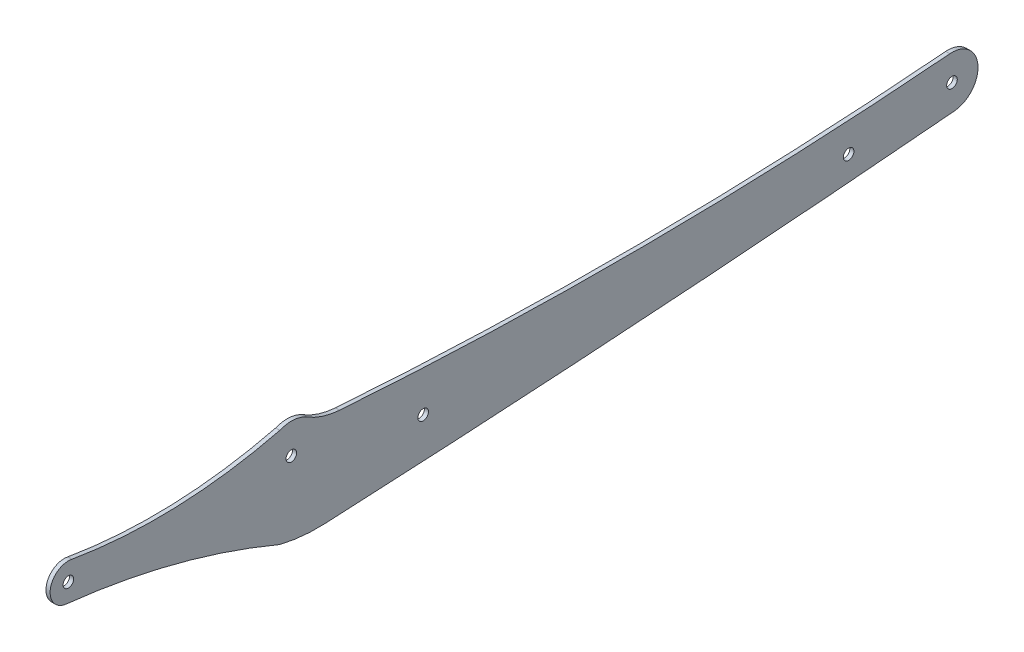
SolidWorks part; units mm, degrees
ref_plane "前基準面" through (0, 0, 0) normal (0, 0, 1) x (1, 0, 0)
ref_plane "上基準面" through (0, 0, 0) normal (0, 1, 0) x (1, 0, 0)
ref_plane "右基準面" through (0, 0, 0) normal (1, 0, 0) x (0, 0, -1)
sketch "草圖1" plane through (0, 0, 0) normal (1, 0, 0) x (0, 0, -1)
  line L0 (-207.7239, 114.2461) -> (-126.7284, 113.3952) construction
  line L1 (-126.7284, 113.3952) -> (113.2584, 110.874) construction
  circle A0 centre (113.2584, 110.874) radius 1.925
  circle A1 centre (-207.7239, 114.2461) radius 1.925
  circle A2 centre (-78.8413, 102.3915) radius 1.925
  circle A3 centre (-126.7284, 113.3952) radius 1.925
  circle A4 centre (75.7163, 107.0681) radius 1.925
  arc A5 (-130.8973, 87.5911) -> (-208.3094, 107.6458) centre (-237.9435, -166.1782) ccw
  arc A6 (-114.3893, 85.9931) -> (114.3939, 101.4797) centre (-375.6591, 5643.3476) ccw
  arc A7 (-114.3893, 85.9931) -> (-130.8973, 87.5911) centre (-117.1128, 143.924) cw
  arc A8 (114.3939, 101.4797) -> (112.4694, 120.3036) centre (113.2584, 110.874) ccw
  arc A9 (-109.2187, 119.0098) -> (112.4694, 120.3036) centre (-6.6895, 1544.3644) ccw
  arc A10 (-121.0531, 122.7744) -> (-109.2187, 119.0098) centre (-107.3148, 145.4788) ccw
  arc A11 (-121.0531, 122.7744) -> (-130.8973, 123.5341) centre (-126.7284, 113.3952) ccw
  arc A12 (-206.4059, 120.7399) -> (-130.8973, 123.5341) centre (-175.3206, 302.3506) ccw
  arc A13 (-206.4059, 120.7399) -> (-208.3094, 107.6458) centre (-207.7239, 114.2461) ccw
  dimension "D1" = 80.9955
  dimension "D2" = 239.9868
extrude "填料-伸長1" add sketch "草圖1" along normal blind 1.5
